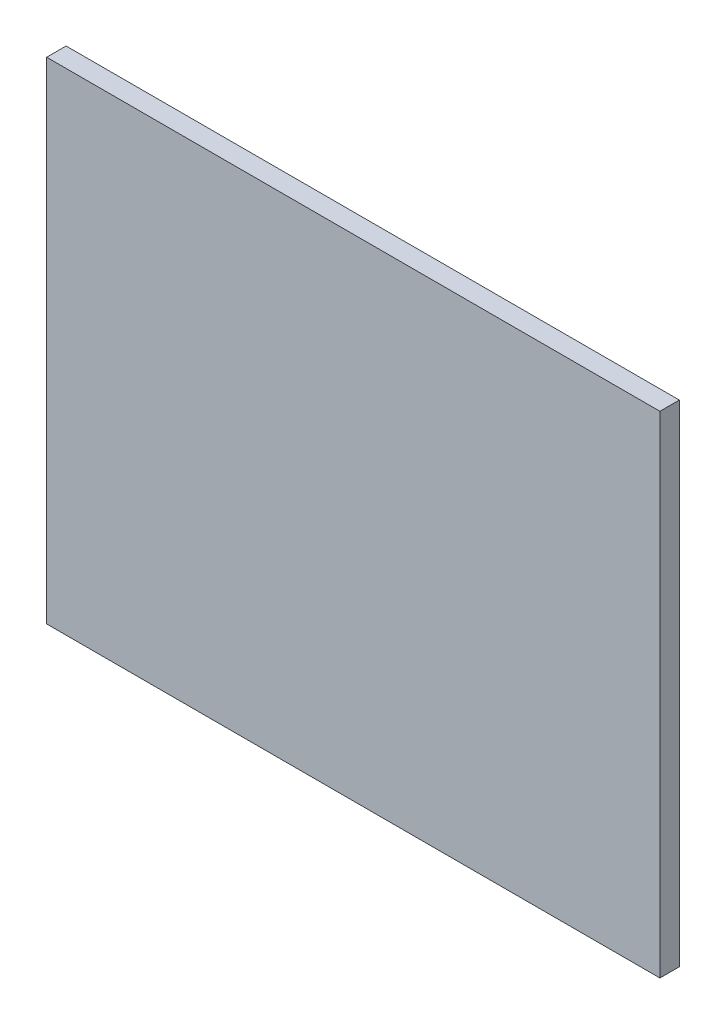
SolidWorks part; units mm, degrees
material "Acrylic (Medium-high impact)"
ref_plane "Front Plane" through (0, 0, 0) normal (0, 0, 1) x (1, 0, 0)
ref_plane "Top Plane" through (0, 0, 0) normal (0, 1, 0) x (1, 0, 0)
ref_plane "Right Plane" through (0, 0, 0) normal (1, 0, 0) x (0, 0, -1)
sketch "Sketch1" plane through (0, 0, 0) normal (0, 0, 1) x (1, 0, 0)
  line L1 (-50.085, 40.085) -> (50.085, 40.085)
  line L2 (-50.085, 40.085) -> (-50.085, -40.085)
  line L3 (-50.085, -40.085) -> (50.085, -40.085)
  line L4 (50.085, 40.085) -> (50.085, -40.085)
  line L5 (-50.085, 40.085) -> (50.085, -40.085) construction
  line L6 (-50.085, -40.085) -> (50.085, 40.085) construction
  point P0 (0, 0)
  dimension "D1" = 100.17
  dimension "D2" = 80.17
extrude "Boss-Extrude1" add sketch "Sketch1" along normal blind 3.175
equation "\"length\"=87.3"
equation "\"D1@Sketch1\"=2*\"kerf\" + 100"
equation "\"width\"=67.3"
equation "\"D2@Sketch1\"=2*\"kerf\" + 80"
equation "\"depth\"=3.175"
equation "\"D1@Boss-Extrude1\"=\"depth\""
equation "\"kerf\"= 0.17 / 2"
